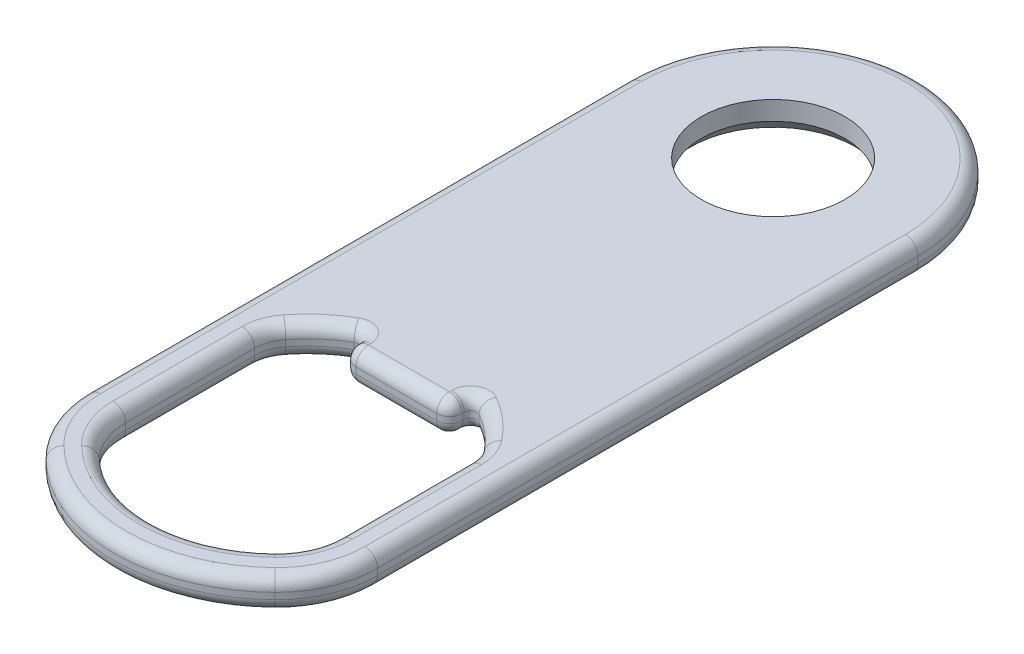
SolidWorks part; units mm, degrees
ref_plane "Front Plane" through (0, 0, 0) normal (0, 0, 1) x (1, 0, 0)
ref_plane "Top Plane" through (0, 0, 0) normal (0, 1, 0) x (1, 0, 0)
ref_plane "Right Plane" through (0, 0, 0) normal (1, 0, 0) x (0, 0, -1)
sketch "Sketch2" plane through (0, 0, 0) normal (1, 0, 0) x (0, 0, -1)
  line L1 (6.5, 3) -> (-6.5, 3) construction
  line L3 (6.5, 11) -> (-6.5, 11)
  dimension "D1" = 8
ref_plane "Plane1" through (0, 11, 0) normal (0, -1, 0) x (0, 0, 1)
sketch "Sketch3" plane through (0, 11, 0) normal (0, -1, 0) x (0, 0, 1)
  line L0 (-5.7, 0) -> (-12, 0)
  line L6 (49.3226, 0) -> (52.3226, 0)
  line L10 (0, 0) -> (0, 20.1636) construction
  line L14 (-12, 0) -> (-12, 11.5)
  line L15 (-12, 0) -> (52.3226, 0) construction
  line L19 (29.9066, 4.2079) -> (29.9066, 0)
  line L20 (27.9066, 4.2079) -> (29.9066, 4.2079)
  line L21 (31.7328, 8.5) -> (44.6183, 8.5)
  line L23 (-12, 11.5) -> (45.4063, 11.5)
  line L24 (5.7, 0) -> (29.9066, 0)
  circle A3 centre (0, 0) radius 5 construction
  arc A4 (5.7, 0) -> (-5.7, 0) centre (0, 0) ccw
  circle A6 centre (0, 0) radius 5.7 construction
  arc A7 (31.7328, 8.5) -> (27.9066, 4.2079) centre (36.9473, 0.0001) ccw
  arc A8 (44.6183, 8.5) -> (49.3226, 0) centre (39.2913, 0) cw
  arc A9 (45.4063, 11.5) -> (52.3226, 0) centre (39.3036, 0) cw
  dimension "D2" = 11.5
  dimension "D3" = 3
  dimension "D1" = 0.7
extrude "Boss-Extrude1" add sketch "Sketch3" against normal blind 2.5
sketch "Sketch5" plane through (0, 11, 0) normal (0, -1, 0) x (0, 0, 1)
  line L0 (45.4063, 11.5) -> (-12, 11.5) construction
  line L3 (0, 11.5) -> (0, 20.0815)
  line L4 (0, 20.0815) -> (-17.2066, 20.0815)
  line L5 (-17.2066, 20.0815) -> (-17.2066, -3.3259)
  line L6 (-17.2066, -3.3259) -> (-11.0086, -3.3259)
  arc A0 (0, 11.5) -> (-11.0086, -3.3259) centre (0, 0) ccw
  arc A1 (5.7, 0) -> (-5.7, 0) centre (0, 0) ccw construction
extrude "Cut-Extrude1" cut sketch "Sketch5" against normal blind 10
fillet "Fillet1" radius 1 1 edges at (-4.2079, 12.25, 29.9066)
fillet "Fillet2" radius 8 1 edges at (-11.5, 12.25, 45.4063)
fillet "Fillet3" radius 5 1 edges at (-8.5, 12.25, 44.6183)
fillet "Fillet4" radius 3 1 edges at (-8.5, 12.25, 31.7328)
fillet "Fillet5" radius 0.5 1 edges at (-4.2079, 12.25, 27.9066)
fillet "Fillet6" radius 1 8 edges at (-4.8997, 11, 51.3654) (-10.8699, 11, 46.0128) (-8.1317, 11, -8.1317) (-4.8997, 13.5, 51.3654) (-10.8699, 13.5, 46.0128) (-8.1317, 13.5, -8.1317) (-11.5, 11, 21.4504) (-11.5, 13.5, 21.4504)
fillet "Fillet7" radius 1 18 edges at (-3.7642, 11, 48.5895) (-8.1039, 11, 44.8562) (-8.5, 11, 37.7841) (-8.3372, 11, 31.6878) (-6.5346, 11, 29.4147) (-4.4571, 11, 28.2956) (-4.2079, 11, 28.8174) (-3.915, 11, 29.6137) (-3.7642, 13.5, 48.5895) (-8.1039, 13.5, 44.8562) (-8.5, 13.5, 37.7841) (-8.3372, 13.5, 31.6878) (-6.5346, 13.5, 29.4147) (-4.4571, 13.5, 28.2956) (-4.2079, 13.5, 28.8174) (-3.915, 13.5, 29.6137) (-1.6039, 11, 29.9066) (-1.6039, 13.5, 29.9066)
chamfer "Chamfer1" distance 1 angle 40 1 edges at (-5.7, 11, 0)
mirror "Mirror1" about plane through (0, 0, 0) normal (1, 0, 0) of bodies 104 101
